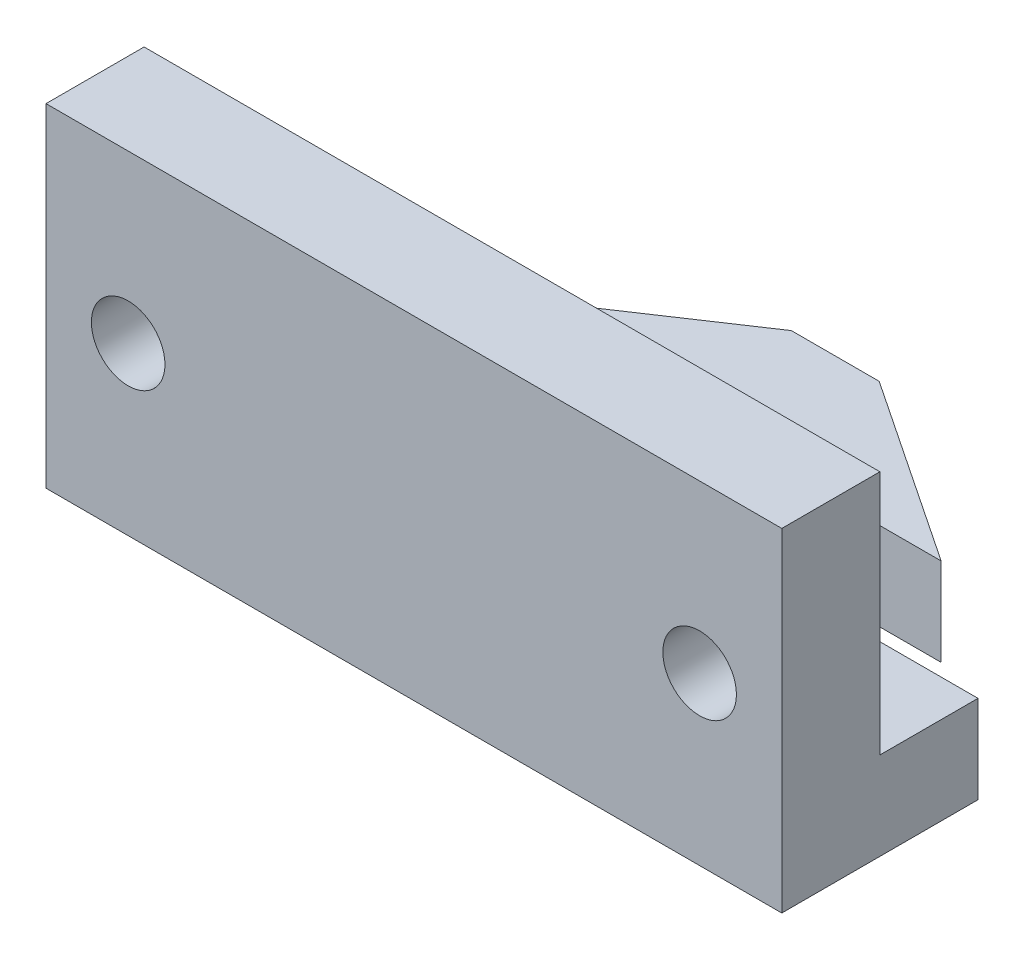
SolidWorks part; units mm, degrees
ref_plane "Front" through (0, 0, 0) normal (0, 0, 1) x (1, 0, 0)
ref_plane "Top" through (0, 0, 0) normal (0, 1, 0) x (1, 0, 0)
ref_plane "Right" through (0, 0, 0) normal (1, 0, 0) x (0, 0, -1)
sketch "Sketch1" plane through (0, 0, 0) normal (0, 1, 0) x (1, 0, 0)
  line L0 (-1.7907, 2.05) -> (-9.398, 2.05)
  line L2 (-1.7907, -2.05) -> (-1.7907, 2.05)
  line L4 (1.7907, -2.05) -> (1.7907, 2.05)
  line L7 (-9.398, 2.05) -> (-1.7907, 7.13)
  line L8 (-1.7907, 7.13) -> (1.7907, 7.13)
  line L9 (1.7907, 7.13) -> (9.398, 2.05)
  line L10 (9.398, 2.05) -> (1.7907, 2.05)
  line L11 (1.7907, -2.05) -> (15, -2.05)
  line L12 (-1.7907, -2.05) -> (-15, -2.05)
  line L13 (-15, -2.05) -> (-15, -10.05)
  line L14 (-15, -10.05) -> (15, -10.05)
  line L15 (15, -10.05) -> (15, -2.05)
  line L16 (15, -2.05) -> (1.7907, -2.05)
  point P0 (0, 0)
  point P17 (0, 7.13)
  point P19 (0, -10.05)
  point P24 (1.7907, 0)
  dimension "D1" = 18.796
  dimension "D2" = 3.5814
  dimension "D3" = 30
  dimension "D4" = 8
  dimension "D5" = 5.08
  dimension "D7" = 4.1
extrude "Boss-Extrude1" add sketch "Sketch1" along normal blind 3.5814 contours L14 L15 L11 L4 L10 L9 L8 L7 L0 L2 L12 L13
sketch "Sketch2" plane through (0, 3.5814, 0) normal (0, 1, 0) x (1, 0, 0)
  line L0 (15, -10.05) -> (15, -2.05) construction
  line L1 (-15, -10.05) -> (15, -10.05)
  line L2 (-15, -10.05) -> (-15, -6.05)
  line L3 (-15, -6.05) -> (15, -6.05)
  line L4 (15, -10.05) -> (15, -6.05)
  dimension "D1" = 4
extrude "Boss-Extrude2" add sketch "Sketch2" along normal blind 10
sketch "Sketch3" plane through (0, 0, 10.05) normal (0, 0, 1) x (1, 0, 0)
  line L0 (-15, 13.5814) -> (-15, 0) construction
  line L1 (-11.65, 6.7907) -> (11.65, 6.7907) construction
  circle A0 centre (-11.65, 6.7907) radius 1.5
  circle A1 centre (11.65, 6.7907) radius 1.5
  point P4 (0, 6.7907)
  point P7 (-15, 6.7907)
  dimension "D1" = 3
  dimension "D2" = 23.3
extrude "Cut-Extrude1" cut sketch "Sketch3" against normal up to vertex (4 mm away)
